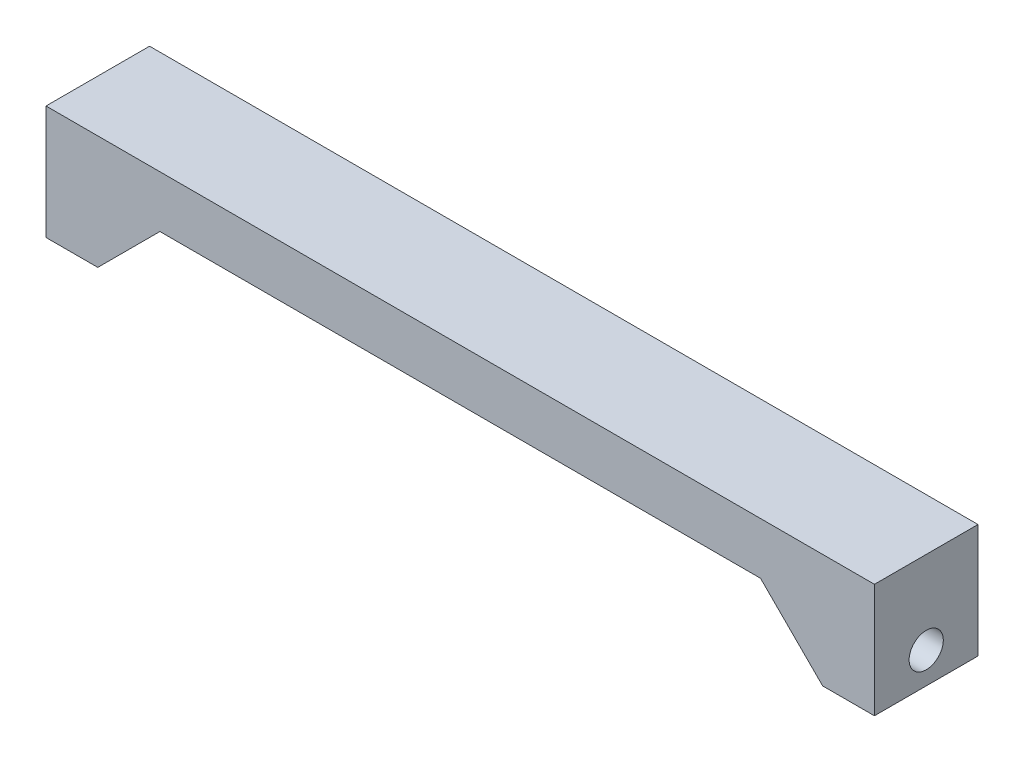
SolidWorks part; units mm, degrees
ref_plane "前视基准面" through (0, 0, 0) normal (0, 0, 1) x (1, 0, 0)
ref_plane "上视基准面" through (0, 0, 0) normal (0, 1, 0) x (1, 0, 0)
ref_plane "右视基准面" through (0, 0, 0) normal (1, 0, 0) x (0, 0, -1)
sketch "草图1" plane through (0, 0, 0) normal (0, 0, 1) x (1, 0, 0)
  line L0 (-40, 0) -> (40, 0)
  line L1 (40, 0) -> (40, -11)
  line L2 (40, -11) -> (35, -11)
  line L3 (35, -11) -> (35, -5)
  line L4 (35, -5) -> (-35, -5)
  line L5 (-35, -5) -> (-35, -11)
  line L6 (-35, -11) -> (-40, -11)
  line L7 (-40, -11) -> (-40, 0)
  line L8 (0, -7.4248) -> (0, 9.2484) construction
  dimension "D1" = 5
  dimension "D2" = 5
  dimension "D3" = 80
  dimension "D4" = 11
  dimension "D5" = 11
extrude "凸台-拉伸2" add sketch "草图1" along normal blind 10
sketch "草图3" plane through (-35, 0, 0) normal (1, 0, 0) x (0, 0, -1)
  line L1 (-10, -11) -> (0, -11) construction
  line L2 (-10, -11) -> (-10, -5) construction
  circle A0 centre (-5, -8) radius 1.65
  dimension "D2" = 3.3
  dimension "D1" = 3
  dimension "D3" = 5
extrude "切除-拉伸1" cut sketch "草图3" against normal through all both and the other way through all
sketch "草图4" plane through (0, 0, 0) normal (0, 0, -1) x (-1, 0, 0)
  line L0 (29, -5) -> (35, -11)
  line L1 (35, -5) -> (-35, -5) construction
  line L2 (29, -5) -> (35, -5)
  line L4 (35, -5) -> (35, -11)
  dimension "D1" = 6
  dimension "D2" = 6
extrude "凸台-拉伸3" add sketch "草图4" against normal blind 2
sketch "草图5" plane through (0, -5, 0) normal (0, -1, 0) x (1, 0, 0)
  line L0 (35, 5) -> (-35, 5) construction
  line L1 (35, 10) -> (35, 0) construction
  line L2 (-35, 10) -> (-35, 2) construction
ref_plane "基准面3" through (0, 0, 5) normal (0, 0, 1) x (1, 0, 0)
mirror "镜向1" about plane through (0, 0, 5) normal (0, 0, 1) of "凸台-拉伸3"
sketch "草图6" plane through (0, 0, 0) normal (0, 1, 0) x (1, 0, 0)
  line L0 (0, -10) -> (0, 0) construction
  line L1 (40, -10) -> (-40, -10) construction
mirror "镜向2" about plane through (0, 0, 0) normal (1, 0, 0) of "镜向1", "凸台-拉伸3"
